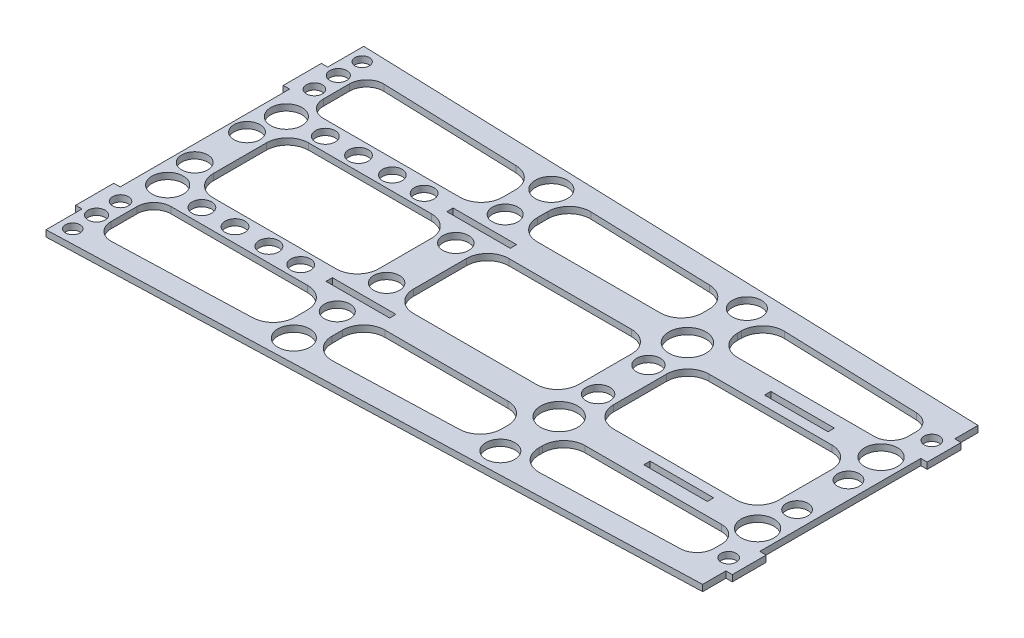
SolidWorks part; units mm, degrees
ref_plane "Front Plane" through (0, 0, 0) normal (0, 0, 1) x (1, 0, 0)
ref_plane "Top Plane" through (0, 0, 0) normal (0, 1, 0) x (1, 0, 0)
ref_plane "Right Plane" through (0, 0, 0) normal (1, 0, 0) x (0, 0, -1)
sketch "Sketch1" plane through (0, 0, 0) normal (0, 1, 0) x (1, 0, 0)
  line L0 (0, 0) -> (0, 75)
  line L7 (0, 75) -> (300, 65)
  line L8 (300, 65) -> (300, 0)
  line L9 (300, 0) -> (0, 0)
  point P0 (0, 0)
  dimension "D4" = 300
  dimension "D5" = 75
  dimension "D6" = 65
extrude "Boss-Extrude1" add sketch "Sketch1" along normal blind 3
mirror "Mirror1" of "Boss-Extrude1"
sketch "Sketch2" plane through (0, 3, 0) normal (0, 1, 0) x (1, 0, 0)
  line L0 (0, -1.65) -> (0, 1.65) construction
  line L1 (0, 31) -> (300, 31) construction
  line L2 (0, 31) -> (0, -31) construction
  line L3 (0, -31) -> (300, -31) construction
  line L4 (300, 31) -> (300, -31) construction
  line L5 (300, -65) -> (300, 65) construction
  line L6 (-1.65, 0) -> (1.65, 0) construction
  line L7 (55.5, 0) -> (150, 0) construction
  line L8 (94.5, -22.5) -> (16.5, -22.5)
  line L9 (94.5, -22.5) -> (94.5, 22.5)
  line L10 (94.5, 22.5) -> (16.5, 22.5)
  line L11 (16.5, -22.5) -> (16.5, 22.5)
  line L12 (94.5, -22.5) -> (16.5, 22.5) construction
  line L13 (94.5, 22.5) -> (16.5, -22.5) construction
  line L14 (189, -22.5) -> (111, -22.5)
  line L15 (189, -22.5) -> (189, 22.5)
  line L16 (189, 22.5) -> (111, 22.5)
  line L17 (111, -22.5) -> (111, 22.5)
  line L18 (189, -22.5) -> (111, 22.5) construction
  line L19 (189, 22.5) -> (111, -22.5) construction
  line L20 (283.5, -22.5) -> (205.5, -22.5)
  line L21 (283.5, -22.5) -> (283.5, 22.5)
  line L22 (283.5, 22.5) -> (205.5, 22.5)
  line L23 (205.5, -22.5) -> (205.5, 22.5)
  line L24 (283.5, -22.5) -> (205.5, 22.5) construction
  line L25 (283.5, 22.5) -> (205.5, -22.5) construction
  line L26 (150, 0) -> (244.5, 0) construction
  line L27 (0, 0) -> (55.5, 0) construction
  line L28 (244.5, 0) -> (300, 0) construction
  line L29 (16.5, -22.5) -> (0, -22.5) construction
  line L30 (94.5, -22.5) -> (111, -22.5) construction
  point P8 (0, 0)
  point P11 (55.5, 0)
  point P16 (150, 0)
  point P21 (244.5, 0)
  dimension "D1" = 62
  dimension "D2" = 45
  dimension "D3" = 78
extrude "Cut-Extrude1" cut sketch "Sketch2" against normal blind 10
fillet "Fillet1" radius 10 12 edges at (283.5, 1.5, 22.5) (94.5, 1.5, 22.5) (189, 1.5, 22.5) (94.5, 1.5, -22.5) (189, 1.5, -22.5) (283.5, 1.5, -22.5) (205.5, 1.5, 22.5) (111, 1.5, 22.5) (16.5, 1.5, 22.5) (16.5, 1.5, -22.5) (111, 1.5, -22.5) (205.5, 1.5, -22.5)
sketch "Sketch3" plane through (0, 3, 0) normal (0, 1, 0) x (1, 0, 0)
  line L0 (-1.65, 0) -> (1.65, 0) construction
  line L1 (-87.6274, -30) -> (294.5978, -30) construction
  line L2 (-87.6274, -30) -> (-87.6274, 30) construction
  line L3 (-87.6274, 30) -> (294.5978, 30) construction
  line L4 (294.5978, -30) -> (294.5978, 30) construction
  line L5 (-87.6274, -30) -> (294.5978, 30) construction
  line L6 (-87.6274, 30) -> (294.5978, -30) construction
  line L7 (12, 56.3233) -> (12, 44)
  line L8 (20, 36) -> (280, 36)
  line L9 (288, 44) -> (288, 47.6567)
  line L10 (280.2665, 55.6522) -> (20.2665, 64.3189)
  line L11 (0, -1.65) -> (0, 1.65) construction
  line L12 (300, -65) -> (300, 65) construction
  line L13 (300, 65) -> (0, 75) construction
  arc A0 (288, 47.6567) -> (280.2665, 55.6522) centre (280, 47.6567) ccw
  arc A1 (280, 36) -> (288, 44) centre (280, 44) ccw
  arc A2 (12, 44) -> (20, 36) centre (20, 44) ccw
  arc A3 (12, 56.3233) -> (20.2665, 64.3189) centre (20, 56.3233) cw
  point P0 (103.4852, 0)
  dimension "D6" = 8
  dimension "D1" = 60
  dimension "D2" = 12
  dimension "D3" = 12
  dimension "D4" = 10
  dimension "D5" = 6
extrude "Cut-Extrude2" cut sketch "Sketch3" against normal blind 10
mirror "Mirror2" about plane through (0, 0, 0) normal (0, 0, 1) of "Cut-Extrude2"
sketch "Sketch4" plane through (0, 3, 0) normal (0, 1, 0) x (1, 0, 0)
  line L0 (-1.65, 0) -> (1.65, 0) construction
  line L1 (94.5, -67.4177) -> (111, -67.4177)
  line L2 (94.5, -67.4177) -> (94.5, 67.4177)
  line L3 (94.5, 67.4177) -> (111, 67.4177)
  line L4 (111, -67.4177) -> (111, 67.4177)
  line L5 (94.5, -67.4177) -> (111, 67.4177) construction
  line L6 (94.5, 67.4177) -> (111, -67.4177) construction
  line L7 (111, 12.5) -> (111, -12.5) construction
  line L8 (94.5, -12.5) -> (94.5, 12.5) construction
  line L9 (205.5, 12.5) -> (205.5, -12.5) construction
  line L10 (189, -63.0534) -> (205.5, -63.0534)
  line L11 (189, -63.0534) -> (189, 63.0534)
  line L12 (189, 63.0534) -> (205.5, 63.0534)
  line L13 (205.5, -63.0534) -> (205.5, 63.0534)
  line L14 (189, -63.0534) -> (205.5, 63.0534) construction
  line L15 (189, 63.0534) -> (205.5, -63.0534) construction
  line L16 (189, -12.5) -> (189, 12.5) construction
  point P0 (102.75, 0)
  point P11 (197.25, 0)
extrude "Boss-Extrude2" add sketch "Sketch4" against normal blind 3
fillet "Fillet2" radius 10 8 edges at (205.5, 1.5, -58.1444) (205.5, 1.5, -36) (189, 1.5, -58.6944) (189, 1.5, -36) (111, 1.5, -61.2944) (111, 1.5, -36) (94.5, 1.5, -36) (94.5, 1.5, -61.8444)
fillet "Fillet3" radius 10 8 edges at (189, 1.5, 58.6944) (94.5, 1.5, 61.8444) (94.5, 1.5, 36) (189, 1.5, 36) (111, 1.5, 61.2944) (205.5, 1.5, 58.1444) (111, 1.5, 36) (205.5, 1.5, 36)
sketch "Sketch5" plane through (0, 3, 0) normal (0, 1, 0) x (1, 0, 0)
  line L0 (300, -65) -> (300, 65) construction
  line L1 (300, 54) -> (303, 54)
  line L2 (300, 54) -> (300, 38)
  line L3 (300, 38) -> (303, 38)
  line L4 (303, 54) -> (303, 38)
  line L5 (0, -1.65) -> (0, 1.65) construction
  line L6 (0, 58) -> (-3, 58)
  line L7 (0, 58) -> (0, 40)
  line L8 (0, 40) -> (-3, 40)
  line L9 (-3, 58) -> (-3, 40)
  line L10 (-1.65, 0) -> (1.65, 0) construction
  line L11 (300, -38) -> (303, -38)
  line L12 (303, -54) -> (303, -38)
  line L13 (300, -54) -> (303, -54)
  line L14 (300, -54) -> (300, -38)
  line L15 (0, -40) -> (-3, -40)
  line L16 (-3, -58) -> (-3, -40)
  line L17 (0, -58) -> (-3, -58)
  line L18 (0, -58) -> (0, -40)
  dimension "D1" = 3
  dimension "D2" = 3
  dimension "D3" = 16
  dimension "D4" = 38
  dimension "D5" = 40
  dimension "D6" = 18
extrude "Boss-Extrude3" add sketch "Sketch5" against normal up to surface (3 mm away) up to face at (247.2105, 0, -46.3677)
sketch "Sketch6" plane through (0, 3, 0) normal (0, 1, 0) x (1, 0, 0)
  line L0 (-1.65, 0) -> (1.65, 0) construction
  line L1 (87.2, 30) -> (117.2, 30)
  line L2 (87.2, 30) -> (87.2, 27)
  line L3 (87.2, 27) -> (117.2, 27)
  line L4 (117.2, 30) -> (117.2, 27)
  line L5 (237.2, 30) -> (267.2, 30)
  line L6 (237.2, 30) -> (237.2, 27)
  line L7 (237.2, 27) -> (267.2, 27)
  line L8 (267.2, 30) -> (267.2, 27)
  line L9 (237.2, -27) -> (267.2, -27)
  line L10 (267.2, -30) -> (267.2, -27)
  line L11 (237.2, -30) -> (267.2, -30)
  line L12 (237.2, -30) -> (237.2, -27)
  line L13 (87.2, -27) -> (117.2, -27)
  line L14 (117.2, -30) -> (117.2, -27)
  line L15 (87.2, -30) -> (117.2, -30)
  line L16 (87.2, -30) -> (87.2, -27)
  line L17 (0, -1.65) -> (0, 1.65) construction
  dimension "D1" = 87.2
  dimension "D2" = 30
  dimension "D3" = 3
  dimension "D4" = 30
  dimension "D5" = 237.2
  dimension "D6" = 27
extrude "Cut-Extrude3" cut sketch "Sketch6" against normal blind 10
sketch "Sketch7" plane through (0, 3, 0) normal (0, 1, 0) x (1, 0, 0)
  line L0 (-1.65, 0) -> (1.65, 0) construction
  circle A0 centre (10.4606, 28.0139) radius 7.3754
  circle A1 centre (102.1398, 39.6352) radius 6.0263
  circle A2 centre (102.7854, 60.7796) radius 7.5362
  circle A3 centre (197.5313, 30.2736) radius 8.7488
  circle A4 centre (197.6927, 58.1971) radius 6.8479
  circle A5 centre (5.9412, 68.3157) radius 3.4151
  circle A6 centre (5.9412, 57.0672) radius 4.0352
  circle A7 centre (5.9412, 45.7687) radius 3.7681
  circle A8 centre (7.5552, 12.3575) radius 6.1526
  circle A9 centre (27.7311, 29.1438) radius 4.6473
  circle A10 centre (43.3876, 29.1438) radius 4.6473
  circle A11 centre (59.3669, 29.1438) radius 4.6473
  circle A12 centre (74.3778, 29.1438) radius 4.6473
  circle A16 centre (102.1398, 16.3259) radius 6.0933
  circle A17 centre (197.5313, 11.8888) radius 5.5794
  circle A18 centre (290.0981, 29.1438) radius 7.7345
  circle A19 centre (291.7186, 12.1203) radius 5.1367
  circle A20 centre (295.2349, 47.9637) radius 3.6121
  circle A21 centre (295.2349, -47.9637) radius 3.6121
  circle A22 centre (291.7186, -12.1203) radius 5.1367
  circle A23 centre (290.0981, -29.1438) radius 7.7345
  circle A24 centre (197.5313, -11.8888) radius 5.5794
  circle A25 centre (102.1398, -16.3259) radius 6.0933
  circle A26 centre (74.3778, -29.1438) radius 4.6473
  circle A27 centre (59.3669, -29.1438) radius 4.6473
  circle A28 centre (43.3876, -29.1438) radius 4.6473
  circle A29 centre (27.7311, -29.1438) radius 4.6473
  circle A30 centre (7.5552, -12.3575) radius 6.1526
  circle A31 centre (5.9412, -45.7687) radius 3.7681
  circle A32 centre (5.9412, -57.0672) radius 4.0352
  circle A33 centre (5.9412, -68.3157) radius 3.4151
  circle A34 centre (197.6927, -58.1971) radius 6.8479
  circle A35 centre (197.5313, -30.2736) radius 8.7488
  circle A36 centre (102.7854, -60.7796) radius 7.5362
  circle A37 centre (102.1398, -39.6352) radius 6.0263
  circle A38 centre (10.4606, -28.0139) radius 7.3754
extrude "Cut-Extrude4" cut sketch "Sketch7" against normal blind 10
